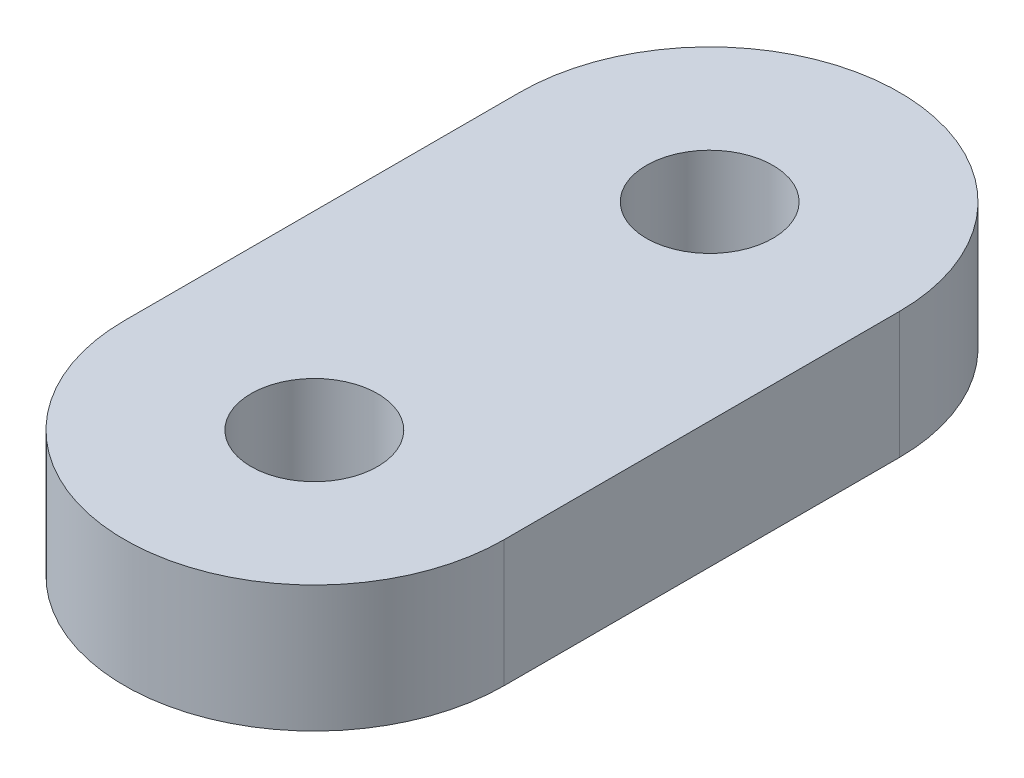
SolidWorks part; units mm, degrees
ref_plane "Front Plane" through (0, 0, 0) normal (0, 0, 1) x (1, 0, 0)
ref_plane "Top Plane" through (0, 0, 0) normal (0, 1, 0) x (1, 0, 0)
ref_plane "Right Plane" through (0, 0, 0) normal (1, 0, 0) x (0, 0, -1)
sketch "Sketch1" plane through (0, 0, 0) normal (0, 1, 0) x (1, 0, 0)
  line L0 (0, 6.25) -> (0, -6.25) construction
  line L1 (6, 6.25) -> (6, -6.25)
  line L2 (-6, 6.25) -> (-6, -6.25)
  arc A0 (6, 6.25) -> (-6, 6.25) centre (0, 6.25) ccw
  arc A1 (-6, -6.25) -> (6, -6.25) centre (0, -6.25) ccw
  point P2 (0, 0)
  dimension "D2" = 6
  dimension "D1" = 12.5
extrude "Boss-Extrude1" add sketch "Sketch1" along normal blind 4
sketch "Sketch2" plane through (0, 4, 0) normal (0, 1, 0) x (1, 0, 0)
  circle A0 centre (0, 6.25) radius 2
  circle A1 centre (0, -6.25) radius 2
  dimension "D1" = 4
  dimension "D2" = 4
extrude "Cut-Extrude3" cut sketch "Sketch2" against normal through all
